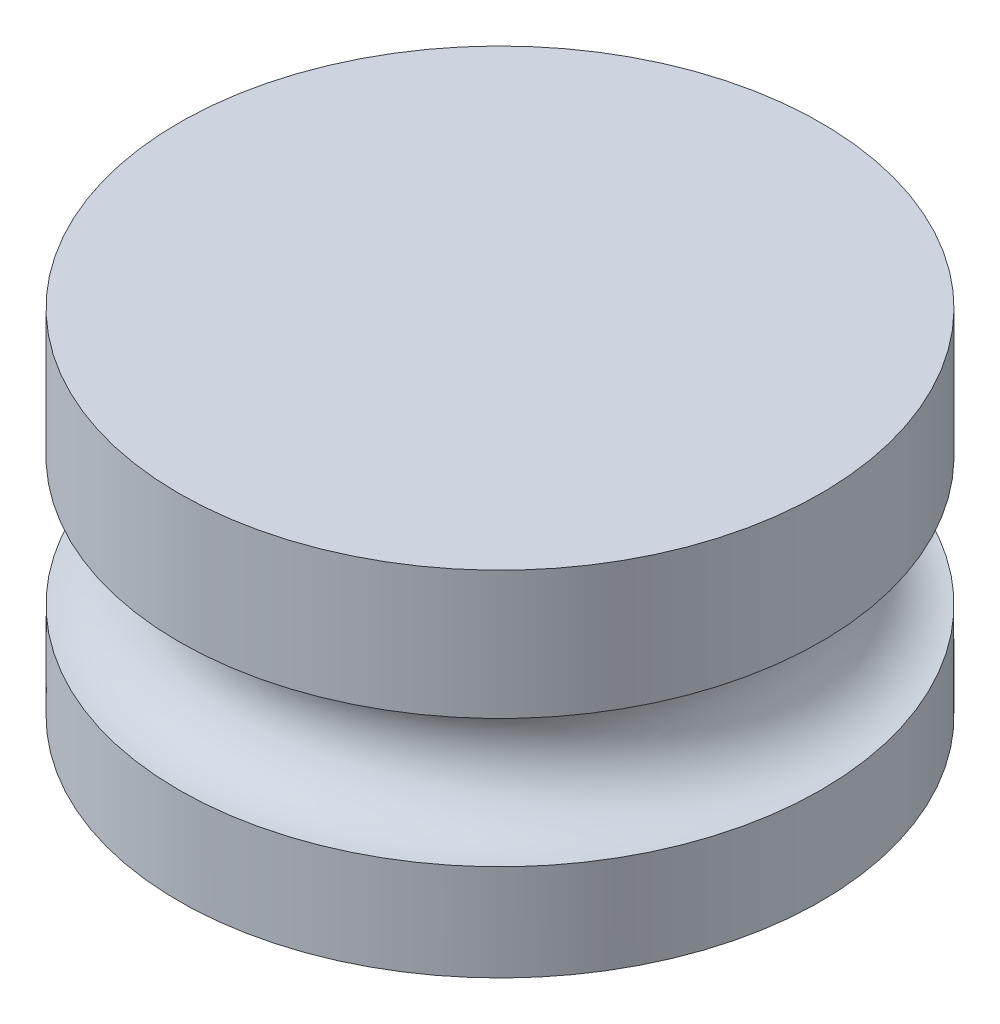
SolidWorks part; units mm, degrees
ref_plane "Front Plane" through (0, 0, 0) normal (0, 0, 1) x (1, 0, 0)
ref_plane "Top Plane" through (0, 0, 0) normal (0, 1, 0) x (1, 0, 0)
ref_plane "Right Plane" through (0, 0, 0) normal (1, 0, 0) x (0, 0, -1)
sketch "Sketch1" plane through (0, 0, 0) normal (0, 1, 0) x (1, 0, 0)
  circle A0 centre (0, 0) radius 5
  circle A1 centre (0, 0) radius 1
  dimension "D1" = 10
  dimension "D2" = 2
extrude "Boss-Extrude1" add sketch "Sketch1" along normal blind 4 contours A0 A1
ref_plane "Plane1" through (0, 2, 0) normal (0, 1, 0) x (1, 0, 0)
sketch "Sketch2" plane through (0, 2, 0) normal (0, 1, 0) x (1, 0, 0)
  circle A0 centre (0, 0) radius 5
  circle A1 centre (0, 0) radius 5
sweep "Cut-Sweep1" cut path "Sketch2" circular profile diameter 2 parameters "D3"=2
sketch "Sketch13" plane through (0, 4, 0) normal (0, 1, 0) x (1, 0, 0)
  circle A0 centre (0, 0) radius 5
  circle A1 centre (0, 0) radius 5 construction
extrude "Boss-Extrude2" add sketch "Sketch13" along normal blind 1
sketch "Sketch14" plane through (0, 0, 0) normal (0, -1, 0) x (1, 0, 0)
  circle A0 centre (0, 0) radius 1
  circle A1 centre (0, 0) radius 5
  circle A2 centre (0, 0) radius 1 construction
  circle A3 centre (0, 0) radius 5 construction
extrude "Boss-Extrude3" add sketch "Sketch14" along normal blind 0.5
